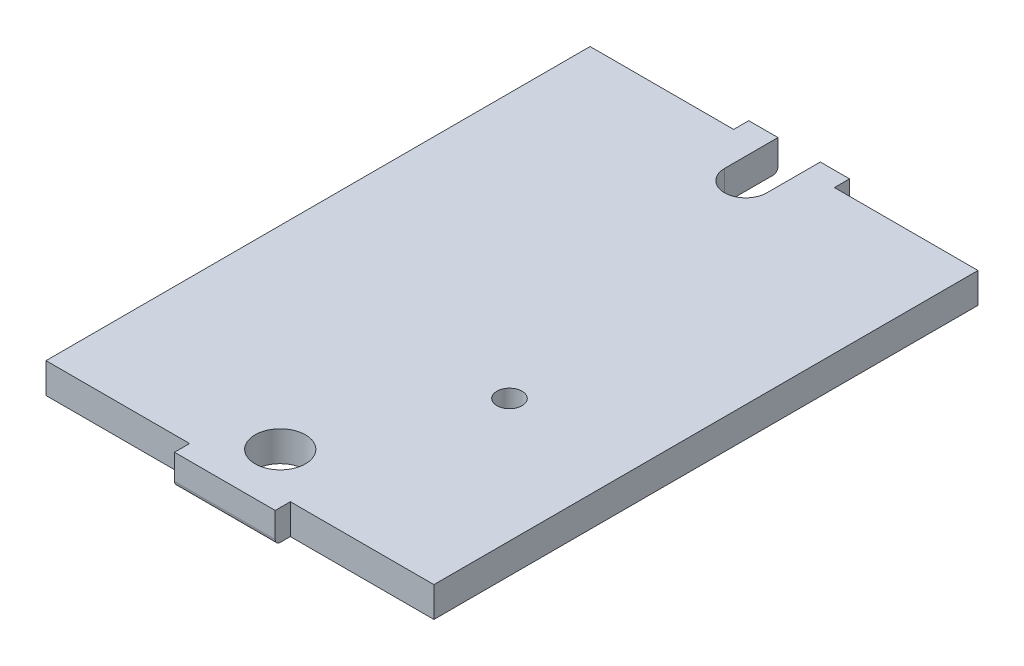
SolidWorks part; units mm, degrees
material "1060 Alloy"
ref_plane "Front Plane" through (0, 0, 0) normal (0, 0, 1) x (1, 0, 0)
ref_plane "Top Plane" through (0, 0, 0) normal (0, 1, 0) x (1, 0, 0)
ref_plane "Right Plane" through (0, 0, 0) normal (1, 0, 0) x (0, 0, -1)
sketch "Sketch1" plane through (0, 0, 0) normal (0, 1, 0) x (1, 0, 0)
  line L0 (0, 27.75) -> (0, 0) construction
  line L1 (-19.25, 27) -> (19.25, 27) construction
  line L2 (-19.25, 27) -> (-19.25, -27)
  line L3 (-19.25, -27) -> (19.25, -27) construction
  line L4 (19.25, 27) -> (19.25, -27)
  line L5 (-19.25, 27) -> (19.25, -27) construction
  line L6 (-19.25, -27) -> (19.25, 27) construction
  line L7 (-5, 27) -> (5, 27) construction
  line L8 (-5, 27) -> (-5, 28.5)
  line L9 (-5, 28.5) -> (5, 28.5)
  line L10 (5, 27) -> (5, 28.5)
  line L11 (-5, 27) -> (5, 28.5) construction
  line L12 (-5, 28.5) -> (5, 27) construction
  line L13 (-19.25, 27) -> (-5, 27)
  line L14 (5, 27) -> (19.25, 27)
  line L15 (0, 0) -> (19.25, 0) construction
  line L16 (5, -27) -> (19.25, -27)
  line L17 (5, -27) -> (5, -28.5)
  line L18 (-5, -28.5) -> (5, -28.5)
  line L19 (-5, -27) -> (-5, -28.5)
  line L20 (-19.25, -27) -> (-5, -27)
  point P0 (0, 0)
  point P10 (0, 27.75)
  dimension "D1" = 54
  dimension "D2" = 38.5
  dimension "D3" = 10
  dimension "D4" = 1.5
extrude "Boss-Extrude1" add sketch "Sketch1" along normal blind 3
fillet "Fillet1" radius 0.5 2 edges at (0, 0, -28.5) (0, 0, 28.5)
sketch "Sketch2" plane through (0, 3, 0) normal (0, 1, 0) x (1, 0, 0)
  line L0 (0, 0) -> (0, -23) construction
  line L1 (-5, -28.5) -> (5, -28.5) construction
  circle A0 centre (0, -23) radius 2.5
  dimension "D1" = 5
  dimension "D2" = 5.5
extrude "Cut-Extrude1" cut sketch "Sketch2" against normal through all contours A0
sketch "Sketch3" plane through (0, 3, 0) normal (0, 1, 0) x (1, 0, 0)
  line L0 (5, 28.5) -> (-5, 28.5) construction
  line L1 (-2.1, 28.5) -> (2.1, 28.5)
  line L2 (-2.1, 28.5) -> (-2.1, 23.2)
  line L3 (-2.1, 23.2) -> (2.1, 23.2) construction
  line L4 (2.1, 28.5) -> (2.1, 23.2)
  line L5 (-2.1, 28.5) -> (2.1, 23.2) construction
  line L6 (-2.1, 23.2) -> (2.1, 28.5) construction
  line L7 (0, 25.85) -> (0, 0) construction
  arc A0 (-2.1, 23.2) -> (2.1, 23.2) centre (0, 23.2) ccw
  point P4 (0, 25.85)
  dimension "D1" = 4.2
  dimension "D2" = 5.3
extrude "Cut-Extrude2" cut sketch "Sketch3" against normal through all
sketch "Sketch4" plane through (0, 3, 0) normal (0, 1, 0) x (1, 0, 0)
  line L0 (5, -27) -> (19.25, -27) construction
  line L1 (19.25, -27) -> (19.25, 27) construction
  circle A0 centre (7, -7.25) radius 1.25
  dimension "D1" = 2.5
  dimension "D2" = 19.75
  dimension "D3" = 12.25
extrude "Cut-Extrude3" cut sketch "Sketch4" against normal through all
chamfer "Chamfer1" distance 0.5 angle 45 1 edges at (7, 0, 8.5)
